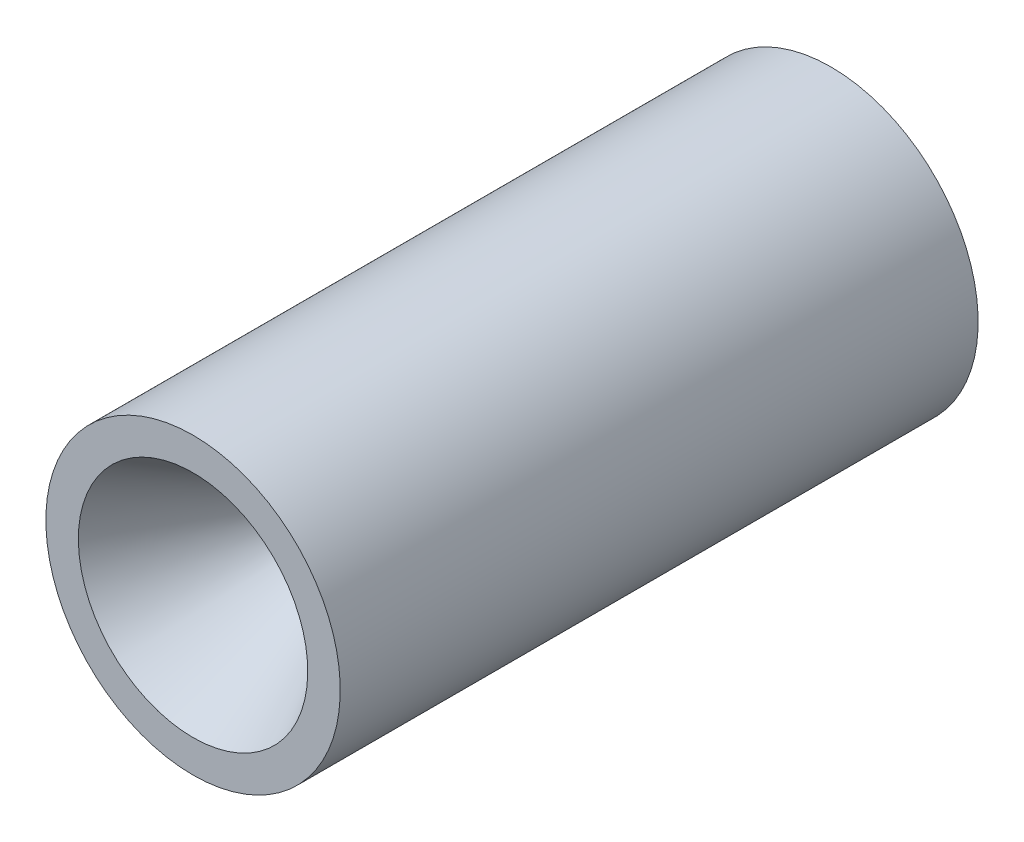
SolidWorks part; units mm, degrees
ref_plane "Front Plane" through (0, 0, 0) normal (0, 0, 1) x (1, 0, 0)
ref_plane "Top Plane" through (0, 0, 0) normal (0, 1, 0) x (1, 0, 0)
ref_plane "Right Plane" through (0, 0, 0) normal (1, 0, 0) x (0, 0, -1)
sketch "Sketch1" plane through (0, 0, 0) normal (1, 0, 0) x (0, 0, -1)
  line L0 (-62.9809, 0) -> (62.9809, 0) construction
  line L1 (-62.9809, 29.689) -> (-28.0559, 9.525)
  line L2 (-28.0559, 9.525) -> (-24.8809, 9.525)
  line L3 (-24.8809, 9.525) -> (102.1191, 33.02)
  line L4 (102.1191, 33.02) -> (102.1191, 38.1)
  line L5 (102.1191, 38.1) -> (-62.9809, 38.1)
  line L6 (-62.9809, 38.1) -> (-62.9809, 29.689)
  point P5 (-87.6628, 85.3652)
  point P10 (0, 0)
  point P11 (0, 0)
  dimension "D1" = 33.02
  dimension "D2" = 38.1
  dimension "D3" = 30
  dimension "D5" = 9.525
  dimension "D6" = 127
  dimension "D7" = 165.1
  dimension "D8" = 38.1
  dimension "D9" = 10.481
  dimension "D10" = 3.175
  dimension "D11" = 125.9617
revolve "Revolve2" add sketch "Sketch1" angle 360 about L0
